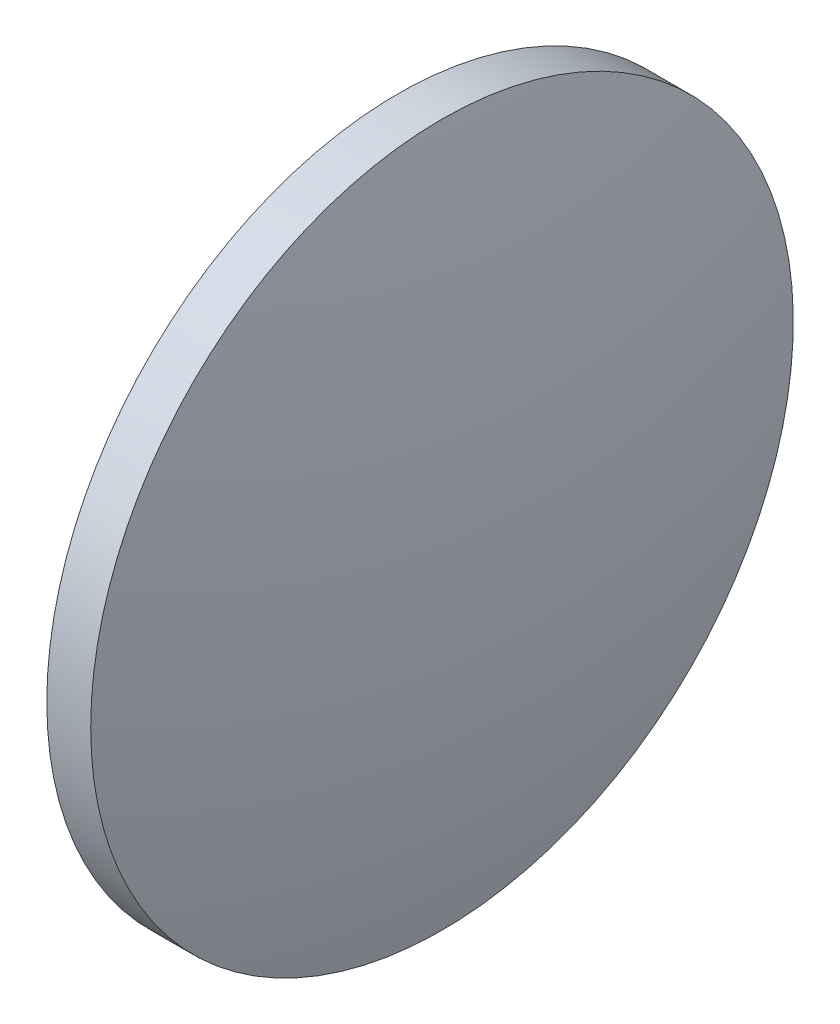
SolidWorks part; units mm, degrees
ref_plane "前视基准面" through (0, 0, 0) normal (0, 0, 1) x (1, 0, 0)
ref_plane "上视基准面" through (0, 0, 0) normal (0, 1, 0) x (1, 0, 0)
ref_plane "右视基准面" through (0, 0, 0) normal (1, 0, 0) x (0, 0, -1)
sketch "草图1" plane through (0, 0, 0) normal (0, 0, 1) x (1, 0, 0)
  line L0 (644.2502, 6.346) -> (663.4264, 6.346) construction
  line L1 (648.9448, 6.346) -> (648.9448, 26.346)
  line L2 (653.9048, 6.346) -> (648.9448, 6.346)
  line L5 (648.9448, 26.346) -> (651.4448, 26.346)
  arc A0 (653.9048, 6.346) -> (651.4448, 26.346) centre (571.3739, 6.346) ccw
revolve "旋转1" add sketch "草图1" angle 360 about L0
